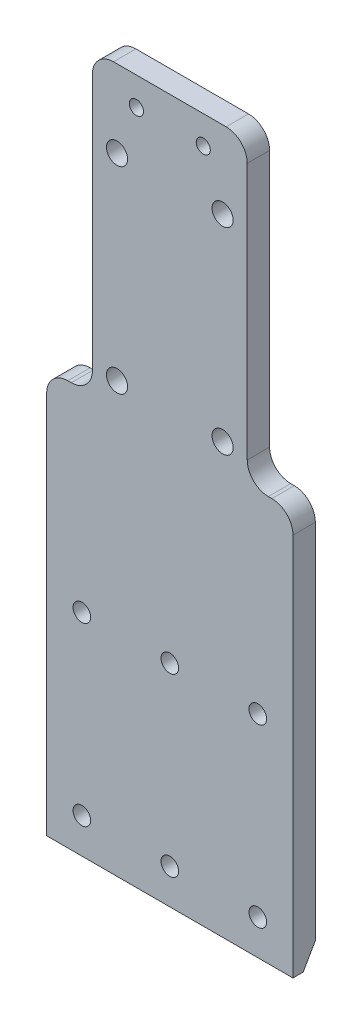
SolidWorks part; units mm, degrees
ref_plane "Front Plane" through (0, 0, 0) normal (0, 0, 1) x (1, 0, 0)
ref_plane "Top Plane" through (0, 0, 0) normal (0, 1, 0) x (1, 0, 0)
ref_plane "Right Plane" through (0, 0, 0) normal (1, 0, 0) x (0, 0, -1)
sketch "Sketch1" plane through (0, 0, 0) normal (0, 0, 1) x (1, 0, 0)
  line L0 (-17.5, 50) -> (17.5, -50) construction
  line L1 (-17.5, 50) -> (17.5, 50)
  line L2 (-17.5, 50) -> (-17.5, -50)
  line L3 (-17.5, -50) -> (17.5, -50)
  line L4 (17.5, 50) -> (17.5, -50)
  dimension "D1" = 35
  dimension "D2" = 100
extrude "Boss-Extrude1" add sketch "Sketch1" along normal blind 3.175
sketch "Sketch2" plane through (0, 0, 3.175) normal (0, 0, 1) x (1, 0, 0)
  line L0 (0, 0) -> (0, 50) construction
  line L1 (17.5, 50) -> (-17.5, 50) construction
  line L2 (-11, 7.5) -> (11, 7.5) construction
  line L3 (-17.5, 50) -> (-11, 50)
  line L4 (-17.5, 50) -> (-17.5, 7.5)
  line L5 (-17.5, 7.5) -> (-11, 7.5)
  line L6 (-11, 50) -> (-11, 7.5)
  line L7 (11, 7.5) -> (17.5, 7.5)
  line L8 (11, 7.5) -> (11, 50)
  line L9 (11, 50) -> (17.5, 50)
  line L10 (17.5, 7.5) -> (17.5, 50)
  line L11 (-7.5, 39) -> (-7.5, 11) construction
  line L12 (-11, 42.5) -> (11, 42.5) construction
  line L13 (-7.5, 25) -> (0, 25) construction
  circle A0 centre (-7.5, 39) radius 1.5
  circle A1 centre (-7.5, 11) radius 1.5
  circle A2 centre (7.5, 11) radius 1.5
  circle A3 centre (7.5, 39) radius 1.5
  point P21 (-3.75, 25)
  dimension "D4" = 3
  dimension "D6" = 15
  dimension "D1" = 22
  dimension "D2" = 35
  dimension "D3" = 7.5
  dimension "D5" = 28
  dimension "D7" = 17.5
extrude "Cut-Extrude1" cut sketch "Sketch2" against normal through all
fillet "Fillet1" radius 3 6 edges at (-17.5, 7.5, 1.5875) (-11, 7.5, 1.5875) (17.5, 7.5, 1.5875) (11, 7.5, 1.5875) (-11, 50, 1.5875) (11, 50, 1.5875)
chamfer "Chamfer1" distance 3 angle 30 1 edges at (0, -50, 0)
sketch "Sketch3" plane through (0, 0, 3.175) normal (0, 0, 1) x (1, 0, 0)
  line L0 (0, 50) -> (0, 46) construction
  line L1 (8, 50) -> (-8, 50) construction
  line L2 (-4.75, 46) -> (4.75, 46) construction
  circle A0 centre (-4.75, 46) radius 1
  circle A1 centre (4.75, 46) radius 1
  dimension "D3" = 2
  dimension "D4" = 2
  dimension "D1" = 9.5
  dimension "D2" = 4
extrude "Cut-Extrude2" cut sketch "Sketch3" against normal through all
sketch "Sketch4" plane through (0, 0, 3.175) normal (0, 0, 1) x (1, 0, 0)
  line L0 (-12.5, -45) -> (12.5, -45) construction
  line L1 (0, -45) -> (0, -50) construction
  line L2 (-17.5, -50) -> (17.5, -50) construction
  line L3 (-12.5, -45) -> (-12.5, -20) construction
  line L4 (-12.5, -20) -> (12.5, -20) construction
  line L5 (12.5, -20) -> (12.5, -45) construction
  line L6 (0, -20) -> (0, -45) construction
  circle A0 centre (-12.5, -45) radius 1.25
  circle A1 centre (12.5, -45) radius 1.25
  circle A2 centre (-12.5, -20) radius 1.25
  circle A3 centre (12.5, -20) radius 1.25
  circle A4 centre (0, -45) radius 1.25
  circle A5 centre (0, -20) radius 1.25
  dimension "D2" = 2.5
  dimension "D1" = 25
  dimension "D3" = 5
  dimension "D4" = 25
extrude "Cut-Extrude3" cut sketch "Sketch4" against normal through all
